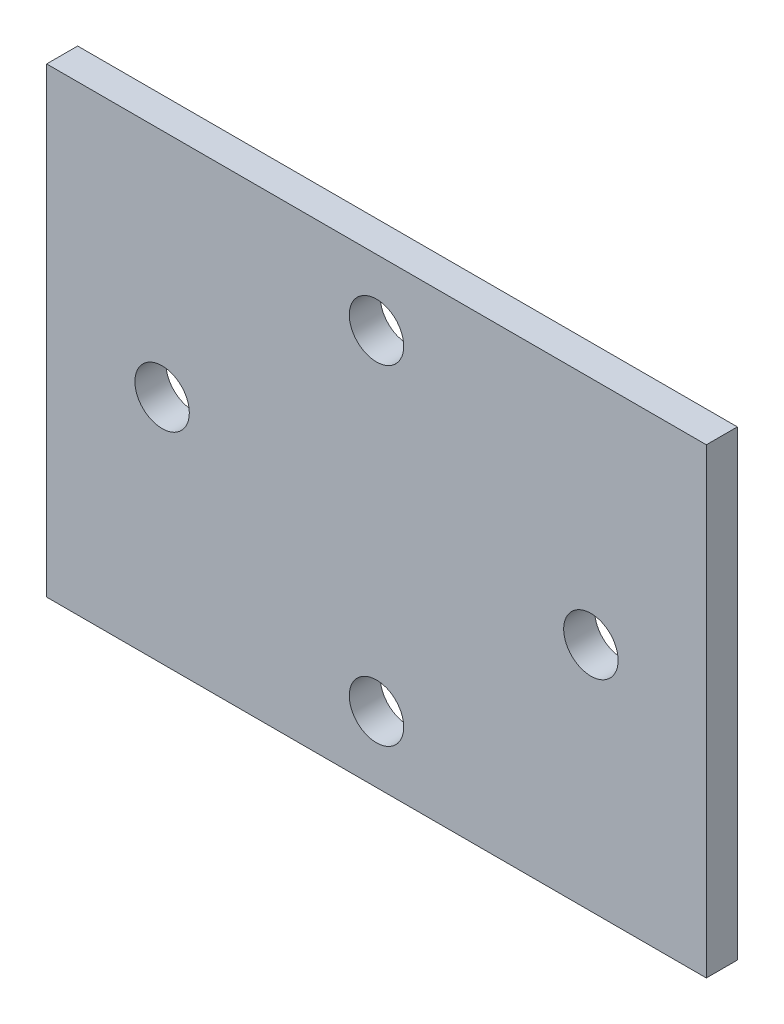
SolidWorks part; units mm, degrees
ref_plane "Front Plane" through (0, 0, 0) normal (0, 0, 1) x (1, 0, 0)
ref_plane "Top Plane" through (0, 0, 0) normal (0, 1, 0) x (1, 0, 0)
ref_plane "Right Plane" through (0, 0, 0) normal (1, 0, 0) x (0, 0, -1)
sketch "Sketch1" plane through (0, 0, 0) normal (0, 0, 1) x (1, 0, 0)
  line L0 (-50.8, -50.8) -> (50.8, -50.8) construction
  line L1 (-50.8, 50.8) -> (-50.8, -50.8) construction
  line L2 (50.8, -50.8) -> (50.8, -25.4) construction
  line L3 (-38.1, -34.8361) -> (-38.1, -41.3639) construction
  point P3 (0, -50.8)
  point P8 (-50.8, 0)
  point P9 (-38.1, -38.1)
  point P10 (50.8, -38.1)
  point P11 (0, 50.8)
  point P12 (-12.7, -38.1)
sketch "Sketch2" plane through (0, 0, 0) normal (1, 0, 0) x (0, 0, -1)
  line L0 (2.3876, 0) -> (-2.3876, 0) construction
  point P4 (0, 0)
  dimension "Thickness" = 4.7752
sketch "Sketch3" plane through (0, 0, 0) normal (0, 0, 1) x (1, 0, 0)
  line L0 (50.8, -25.4) -> (50.8, -50.8)
  line L1 (50.8, -50.8) -> (-50.8, -50.8)
  line L2 (-50.8, -50.8) -> (-50.8, 50.8)
  line L3 (-50.8, 50.8) -> (-25.4, 50.8)
  line L4 (-25.4, 50.8) -> (50.8, -25.4)
extrude "Boss-Extrude1" add sketch "Sketch3" against normal up to vertex (2.3876 mm away) and the other way up to vertex (2.3876 mm away) up to point (0, 0, -2.3876) other way up to point (0, 0, 2.3876)
sketch "Sketch4" plane through (0, 0, 2.3876) normal (0, 0, 1) x (1, 0, 0)
  line L0 (-38.1, -34.8361) -> (-38.1, -41.3639) construction
  line L1 (-50.8, -50.8) -> (0, 0) construction
  line L2 (-38.1, -38.1) -> (-12.7, -38.1) construction
  line L3 (-38.1, -38.1) -> (-38.1, -12.7) construction
  circle A0 centre (-38.1, -38.1) radius 3.2639
  circle A5 centre (-12.7, -38.1) radius 3.2639
  circle A6 centre (12.7, -38.1) radius 3.2639
  circle A7 centre (-38.1, -12.7) radius 3.2639
  circle A8 centre (-38.1, 12.7) radius 3.2639
  circle A9 centre (38.1, -38.1) radius 3.2639
  circle A10 centre (-38.1, 38.1) radius 3.2639
  dimension "D2" = 25.4
  dimension "D4" = 25.4
  dimension "D1" = 4
  dimension "D3" = 4
extrude "Cut-Extrude1" cut sketch "Sketch4" against normal through all
sketch "Sketch7" plane through (0, 0, 2.3876) normal (0, 0, 1) x (1, 0, 0)
  line L0 (50.8, -50.8) -> (50.8, -25.4) construction
  line L1 (-50.8, -50.8) -> (50.8, -50.8)
  line L2 (-50.8, -50.8) -> (-50.8, 50.8)
  line L3 (-50.8, 50.8) -> (50.8, 50.8)
  line L4 (50.8, -50.8) -> (50.8, 50.8)
extrude "Boss-Extrude2" add sketch "Sketch7" against normal up to surface (4.7752 mm away) up to face at (-9.4361, -38.1, -2.3876)
sketch "Sketch10" plane through (0, 0, 2.3876) normal (0, 0, 1) x (1, 0, 0)
  line L0 (0, 0) -> (-80.2914, 0) construction
  circle A0 centre (-33.02, 0) radius 4.191
  circle A1 centre (33.02, 0) radius 4.191
  circle A2 centre (0, 25.4) radius 4.191
  circle A3 centre (0, -25.4) radius 4.191
  dimension "D1" = 8.382
  dimension "D4" = 8.382
  dimension "D2" = 33.02
  dimension "D3" = 33.02
  dimension "D5" = 25.4
extrude "Cut-Extrude3" cut sketch "Sketch10" against normal through all
sketch "Sketch11" plane through (0, 0, 2.3876) normal (0, 0, 1) x (1, 0, 0)
  line L0 (50.8, -50.8) -> (50.8, 50.8) construction
  line L1 (-50.8, -35.56) -> (50.8, -35.56)
  line L2 (-50.8, -35.56) -> (-50.8, 35.56)
  line L3 (-50.8, 35.56) -> (50.8, 35.56)
  line L4 (50.8, -35.56) -> (50.8, 35.56)
  line L5 (-50.8, -35.56) -> (50.8, 35.56) construction
  line L6 (-50.8, 35.56) -> (50.8, -35.56) construction
  line L7 (50.8, 50.8) -> (-50.8, 50.8) construction
  point P0 (0, 0)
  dimension "D1" = 15.24
extrude "Cut-Extrude4" cut sketch "Sketch11" against normal up to next (4.7752 mm away) flip side to cut
equation "\"D2@Sketch4\"=\"Hole Spacing@Sketch1\""
equation "\"D1@Sketch4\"=\"#Holes@Sketch1\""
equation "\"D4@Sketch4\"=\"Hole Spacing@Sketch1\""
equation "\"D3@Sketch4\"=\"#Holes@Sketch1\""
equation "\"D3@Sketch10\"=\"D2@Sketch10\""
